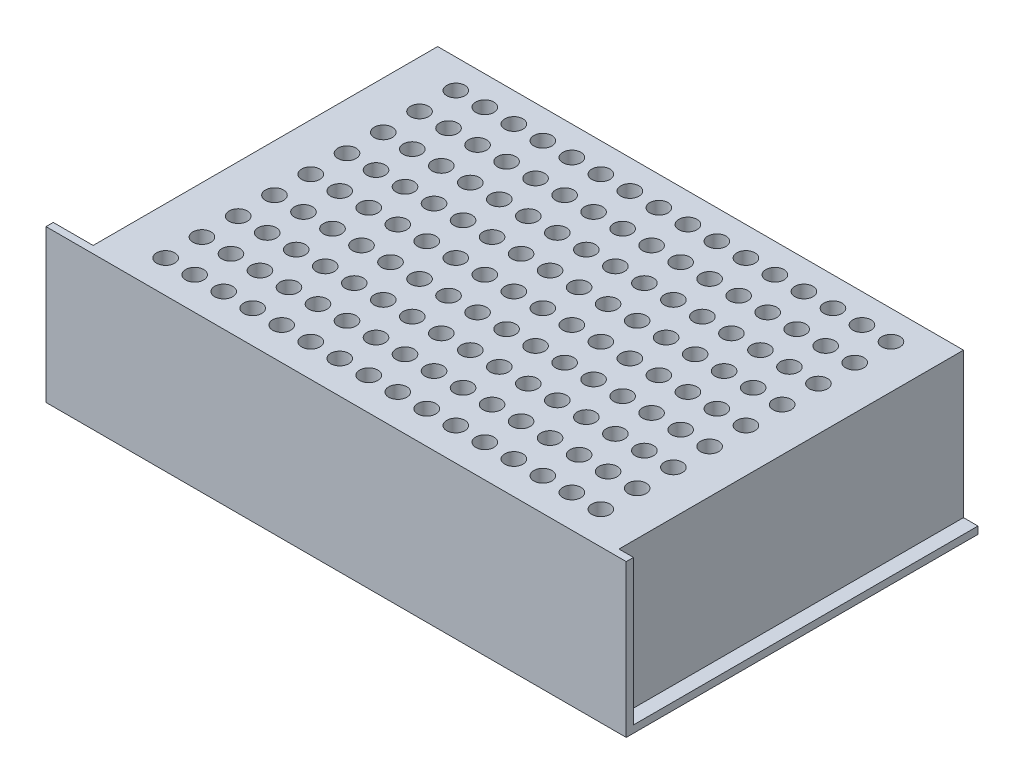
SolidWorks part; units mm, degrees
ref_plane "前视基准面" through (0, 0, 0) normal (0, 0, 1) x (1, 0, 0)
ref_plane "上视基准面" through (0, 0, 0) normal (0, 1, 0) x (1, 0, 0)
ref_plane "右视基准面" through (0, 0, 0) normal (1, 0, 0) x (0, 0, -1)
sketch "草图2" plane through (0, 0, 0) normal (1, 0, 0) x (0, 0, -1)
  line L0 (0, 0) -> (-97, 0)
  line L1 (-97, 0) -> (-97, 42)
  line L2 (-97, 42) -> (-95, 42)
  line L3 (-95, 42) -> (-95, 2)
  line L4 (-95, 2) -> (0, 2)
  line L5 (0, 2) -> (0, 0)
  dimension "D1" = 2
  dimension "D2" = 2
  dimension "D3" = 97
  dimension "D4" = 42
extrude "凸台-拉伸1" add sketch "草图2" along normal blind 160
sketch "草图3" plane through (0, 2, 0) normal (0, 1, 0) x (1, 0, 0)
  line L0 (160, 0) -> (0, 0) construction
  line L1 (156, 0) -> (11, 0)
  line L2 (156, 0) -> (156, -95)
  line L3 (156, -95) -> (11, -95)
  line L4 (11, 0) -> (11, -95)
  line L5 (160, -95) -> (0, -95) construction
  line L6 (160, 0) -> (160, -95) construction
  dimension "D1" = 4
  dimension "D2" = 145
extrude "凸台-拉伸2" add sketch "草图3" along normal blind 40
sketch "草图4" plane through (0, 42, 0) normal (0, 1, 0) x (1, 0, 0)
  line L0 (156, 0) -> (11, 0) construction
  line L1 (11, 0) -> (11, -95) construction
  circle A0 centre (24, -8) radius 2.5
  circle A1 centre (32, -8) radius 2.5
  circle A2 centre (40, -8) radius 2.5
  circle A3 centre (48, -8) radius 2.5
  circle A4 centre (56, -8) radius 2.5
  circle A5 centre (64, -8) radius 2.5
  circle A6 centre (72, -8) radius 2.5
  circle A7 centre (80, -8) radius 2.5
  circle A8 centre (88, -8) radius 2.5
  circle A9 centre (96, -8) radius 2.5
  circle A10 centre (104, -8) radius 2.5
  circle A11 centre (112, -8) radius 2.5
  circle A12 centre (120, -8) radius 2.5
  circle A13 centre (128, -8) radius 2.5
  circle A14 centre (136, -8) radius 2.5
  circle A15 centre (144, -8) radius 2.5
  circle A16 centre (32, -18) radius 2.5
  circle A17 centre (40, -18) radius 2.5
  circle A18 centre (48, -18) radius 2.5
  circle A19 centre (56, -18) radius 2.5
  circle A20 centre (64, -18) radius 2.5
  circle A21 centre (72, -18) radius 2.5
  circle A22 centre (80, -18) radius 2.5
  circle A23 centre (88, -18) radius 2.5
  circle A24 centre (96, -18) radius 2.5
  circle A25 centre (104, -18) radius 2.5
  circle A26 centre (112, -18) radius 2.5
  circle A27 centre (120, -18) radius 2.5
  circle A28 centre (128, -18) radius 2.5
  circle A29 centre (136, -18) radius 2.5
  circle A30 centre (144, -18) radius 2.5
  circle A31 centre (32, -28) radius 2.5
  circle A32 centre (40, -28) radius 2.5
  circle A33 centre (48, -28) radius 2.5
  circle A34 centre (56, -28) radius 2.5
  circle A35 centre (64, -28) radius 2.5
  circle A36 centre (72, -28) radius 2.5
  circle A37 centre (80, -28) radius 2.5
  circle A38 centre (88, -28) radius 2.5
  circle A39 centre (96, -28) radius 2.5
  circle A40 centre (104, -28) radius 2.5
  circle A41 centre (112, -28) radius 2.5
  circle A42 centre (120, -28) radius 2.5
  circle A43 centre (128, -28) radius 2.5
  circle A44 centre (136, -28) radius 2.5
  circle A45 centre (144, -28) radius 2.5
  circle A46 centre (32, -38) radius 2.5
  circle A47 centre (40, -38) radius 2.5
  circle A48 centre (48, -38) radius 2.5
  circle A49 centre (56, -38) radius 2.5
  circle A50 centre (64, -38) radius 2.5
  circle A51 centre (72, -38) radius 2.5
  circle A52 centre (80, -38) radius 2.5
  circle A53 centre (88, -38) radius 2.5
  circle A54 centre (96, -38) radius 2.5
  circle A55 centre (104, -38) radius 2.5
  circle A56 centre (112, -38) radius 2.5
  circle A57 centre (120, -38) radius 2.5
  circle A58 centre (128, -38) radius 2.5
  circle A59 centre (136, -38) radius 2.5
  circle A60 centre (144, -38) radius 2.5
  circle A61 centre (32, -48) radius 2.5
  circle A62 centre (40, -48) radius 2.5
  circle A63 centre (48, -48) radius 2.5
  circle A64 centre (56, -48) radius 2.5
  circle A65 centre (64, -48) radius 2.5
  circle A66 centre (72, -48) radius 2.5
  circle A67 centre (80, -48) radius 2.5
  circle A68 centre (88, -48) radius 2.5
  circle A69 centre (96, -48) radius 2.5
  circle A70 centre (104, -48) radius 2.5
  circle A71 centre (112, -48) radius 2.5
  circle A72 centre (120, -48) radius 2.5
  circle A73 centre (128, -48) radius 2.5
  circle A74 centre (136, -48) radius 2.5
  circle A75 centre (144, -48) radius 2.5
  circle A76 centre (32, -58) radius 2.5
  circle A77 centre (40, -58) radius 2.5
  circle A78 centre (48, -58) radius 2.5
  circle A79 centre (56, -58) radius 2.5
  circle A80 centre (64, -58) radius 2.5
  circle A81 centre (72, -58) radius 2.5
  circle A82 centre (80, -58) radius 2.5
  circle A83 centre (88, -58) radius 2.5
  circle A84 centre (96, -58) radius 2.5
  circle A85 centre (104, -58) radius 2.5
  circle A86 centre (112, -58) radius 2.5
  circle A87 centre (120, -58) radius 2.5
  circle A88 centre (128, -58) radius 2.5
  circle A89 centre (136, -58) radius 2.5
  circle A90 centre (144, -58) radius 2.5
  circle A91 centre (32, -68) radius 2.5
  circle A92 centre (40, -68) radius 2.5
  circle A93 centre (48, -68) radius 2.5
  circle A94 centre (56, -68) radius 2.5
  circle A95 centre (64, -68) radius 2.5
  circle A96 centre (72, -68) radius 2.5
  circle A97 centre (80, -68) radius 2.5
  circle A98 centre (88, -68) radius 2.5
  circle A99 centre (96, -68) radius 2.5
  circle A100 centre (104, -68) radius 2.5
  circle A101 centre (112, -68) radius 2.5
  circle A102 centre (120, -68) radius 2.5
  circle A103 centre (128, -68) radius 2.5
  circle A104 centre (136, -68) radius 2.5
  circle A105 centre (144, -68) radius 2.5
  circle A106 centre (32, -78) radius 2.5
  circle A107 centre (40, -78) radius 2.5
  circle A108 centre (48, -78) radius 2.5
  circle A109 centre (56, -78) radius 2.5
  circle A110 centre (64, -78) radius 2.5
  circle A111 centre (72, -78) radius 2.5
  circle A112 centre (80, -78) radius 2.5
  circle A113 centre (88, -78) radius 2.5
  circle A114 centre (96, -78) radius 2.5
  circle A115 centre (104, -78) radius 2.5
  circle A116 centre (112, -78) radius 2.5
  circle A117 centre (120, -78) radius 2.5
  circle A118 centre (128, -78) radius 2.5
  circle A119 centre (136, -78) radius 2.5
  circle A120 centre (144, -78) radius 2.5
  circle A121 centre (32, -88) radius 2.5
  circle A122 centre (40, -88) radius 2.5
  circle A123 centre (48, -88) radius 2.5
  circle A124 centre (56, -88) radius 2.5
  circle A125 centre (64, -88) radius 2.5
  circle A126 centre (72, -88) radius 2.5
  circle A127 centre (80, -88) radius 2.5
  circle A128 centre (88, -88) radius 2.5
  circle A129 centre (96, -88) radius 2.5
  circle A130 centre (104, -88) radius 2.5
  circle A131 centre (112, -88) radius 2.5
  circle A132 centre (120, -88) radius 2.5
  circle A133 centre (128, -88) radius 2.5
  circle A134 centre (136, -88) radius 2.5
  circle A135 centre (144, -88) radius 2.5
  circle A136 centre (24, -18) radius 2.5
  circle A137 centre (24, -28) radius 2.5
  circle A138 centre (24, -38) radius 2.5
  circle A139 centre (24, -48) radius 2.5
  circle A140 centre (24, -58) radius 2.5
  circle A141 centre (24, -68) radius 2.5
  circle A142 centre (24, -78) radius 2.5
  circle A143 centre (24, -88) radius 2.5
  dimension "D1" = 5
  dimension "D4" = 8
  dimension "D5" = 13
  dimension "D2" = 16
  dimension "D3" = 9
extrude "切除-拉伸1" cut sketch "草图4" against normal blind 20
sketch "草图5" plane through (11, 0, 0) normal (-1, 0, 0) x (0, 0, 1)
  line L0 (95, 2) -> (95, 42) construction
  line L1 (10, 10.8368) -> (79, 10.8368)
  line L2 (10, 10.8368) -> (10, 27.8368)
  line L3 (10, 27.8368) -> (79, 27.8368)
  line L4 (79, 10.8368) -> (79, 27.8368)
  dimension "D1" = 16
  dimension "69" = 69
  dimension "D2" = 17
extrude "凸台-拉伸3" add sketch "草图5" along normal blind 12
sketch "草图6" plane through (0, 0, 0) normal (0, -1, 0) x (1, 0, 0)
  line L0 (24, 65) -> (102, 65) construction
  line L2 (0, 97) -> (0, 0) construction
  line L4 (160, 0) -> (0, 0) construction
  circle A0 centre (102, 65) radius 1.5
  circle A1 centre (24, 65) radius 1.5
  dimension "D1" = 3
  dimension "D2" = 3
  dimension "D3" = 78
  dimension "D4" = 24
  dimension "D5" = 65
extrude "切除-安装孔" cut sketch "草图6" against normal blind 12
